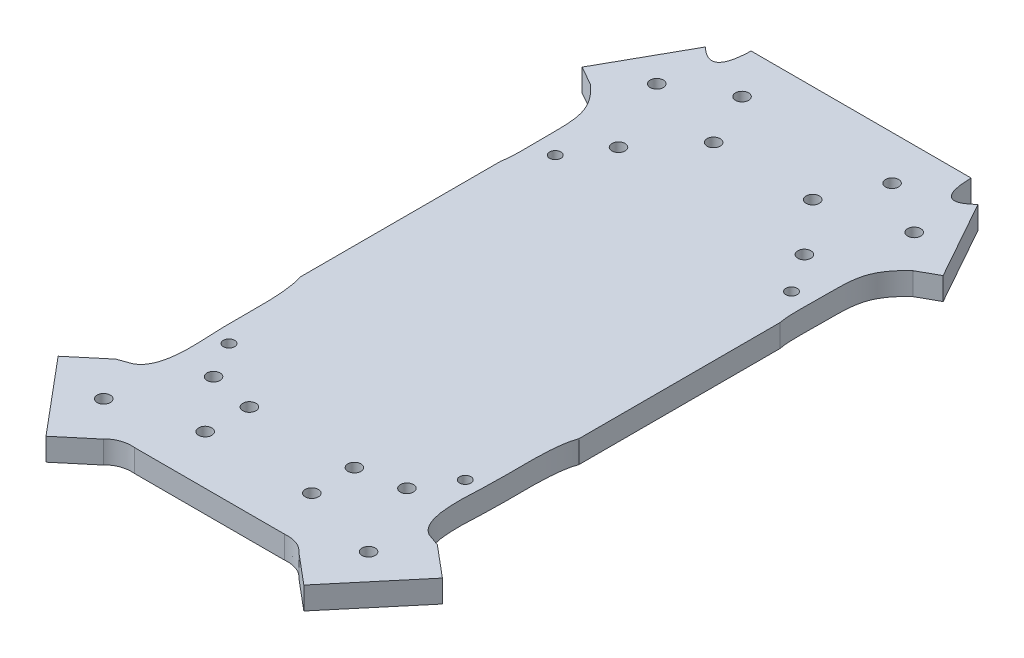
SolidWorks part; units mm, degrees
ref_plane "Front Plane" through (0, 0, 0) normal (0, 0, 1) x (1, 0, 0)
ref_plane "Top Plane" through (0, 0, 0) normal (0, 1, 0) x (1, 0, 0)
ref_plane "Right Plane" through (0, 0, 0) normal (1, 0, 0) x (0, 0, -1)
sketch "Sketch1" plane through (0, 0, 0) normal (0, 1, 0) x (1, 0, 0)
  line L1 (0, 0) -> (200, 0)
  line L2 (0, 0) -> (0, 250)
  line L3 (0, 250) -> (200, 250)
  line L4 (200, 0) -> (200, 250)
  dimension "D1" = 250
  dimension "D2" = 200
extrude "Boss-Extrude1" add sketch "Sketch1" along normal blind 6
hole_wizard "Ø3.0mm Dowel Hole1" positions "Sketch4" profile "Sketch5" hole size "Ø3.0" standard "ANSI Metric" end condition through all
sketch "Sketch4" plane through (0, 0, 0) normal (0, -1, 0) x (-1, 0, 0)
  point P0 (-83.2968, 150.1379)
  point P3 (-94.867, 163.9267)
  point P6 (-121.2968, 163.9267)
  point P9 (-132.867, 150.1379)
  point P12 (-128.0819, 178.2926)
  point P15 (-142.4028, 169.8881)
  point P18 (-88.0819, 178.2926)
  point P21 (-73.761, 169.8881)
  point P24 (-133.867, 43.1379)
  point P27 (-122.0819, 40.922)
  point P30 (-122.2968, 29.3491)
  point P33 (-94.0819, 40.922)
  point P36 (-93.867, 29.3491)
  point P39 (-82.2968, 43.1379)
  point P42 (-72.761, 23.3877)
  point P45 (-143.4028, 23.3877)
  point P51 (-128.0819, 170.5038)
  point P56 (-72.3135, 72.4419)
  point P61 (-77.6564, 46.709)
  dimension "D1" = 9.5358
  dimension "D2" = 19.7502
  dimension "D3" = 14.3209
  dimension "D4" = 8.4046
  dimension "D5" = 14.3659
  dimension "D6" = 6.7851
  dimension "D7" = 26.4298
  dimension "D8" = 14.3659
  dimension "D9" = 14.3209
  dimension "D10" = 8.4046
  dimension "D11" = 19.7502
  dimension "D12" = 9.5358
  dimension "D13" = 11.5702
  dimension "D14" = 13.7888
  dimension "D15" = 11.7851
  dimension "D16" = 2.2159
  dimension "D17" = 11.5729
  dimension "D18" = 21.106
  dimension "D19" = 5.9614
  dimension "D20" = 21.3209
  dimension "D21" = 11.5729
  dimension "D22" = 11.5702
  dimension "D23" = 11.7851
  dimension "D24" = 2.2159
  dimension "D25" = 19.7502
  dimension "D26" = 9.5358
  dimension "D27" = 28
  dimension "D28" = 11.5729
  dimension "D29" = 107
sketch "Sketch5" plane through (83.2968, 0, -150.1379) normal (1, 0, 0) x (0, 0, -1)
  line L0 (0, 0) -> (0, 6)
  line L1 (0, 6) -> (1.75, 6)
  line L2 (1.75, 6) -> (1.75, 0)
  line L5 (1.75, 0) -> (0, 0)
  line L11 (0, -6.35) -> (0, 107.95) construction
  dimension "Thru Hole Dia." = 3.5
  dimension "Thru Hole Depth" = 6
sketch "Sketch6" plane through (0, 0, 0) normal (0, -1, 0) x (1, 0, 0)
  line L0 (125.0968, -27.7325) -> (122.2968, -26.1159)
  line L1 (122.2968, -26.1159) -> (119.4968, -27.7325)
  line L2 (119.4968, -27.7325) -> (119.4968, -30.9657)
  line L3 (132.867, -153.3711) -> (132.867, -146.9047) construction
  line L4 (135.667, -150.1379) -> (130.067, -150.1379) construction
  line L5 (119.4968, -30.9657) -> (122.2968, -32.5823)
  line L6 (122.2968, -32.5823) -> (125.0968, -30.9657)
  line L7 (125.0968, -30.9657) -> (125.0968, -27.7325)
  line L8 (133.867, -39.9047) -> (131.067, -41.5213)
  line L9 (131.067, -41.5213) -> (131.067, -44.7545)
  line L10 (131.067, -44.7545) -> (133.867, -46.3711)
  line L11 (133.867, -46.3711) -> (136.667, -44.7545)
  line L12 (136.667, -44.7545) -> (136.667, -41.5213)
  line L13 (136.667, -41.5213) -> (133.867, -39.9047)
  line L19 (121.2968, -167.1599) -> (121.2968, -160.6935) construction
  line L22 (82.2968, -39.9047) -> (79.4968, -41.5213)
  line L23 (79.4968, -41.5213) -> (79.4968, -44.7545)
  line L24 (79.4968, -44.7545) -> (82.2968, -46.3711)
  line L25 (118.4968, -163.9267) -> (124.0968, -163.9267) construction
  line L26 (82.2968, -46.3711) -> (85.0968, -44.7545)
  line L27 (85.0968, -44.7545) -> (85.0968, -41.5213)
  line L28 (94.867, -167.1599) -> (94.867, -160.6935) construction
  line L29 (97.667, -163.9267) -> (92.067, -163.9267) construction
  line L30 (85.0968, -41.5213) -> (82.2968, -39.9047)
  line L31 (93.867, -26.1159) -> (91.067, -27.7325)
  line L32 (83.2968, -153.3711) -> (83.2968, -146.9047) construction
  line L33 (80.4968, -148.5213) -> (86.0968, -151.7545) construction
  line L34 (91.067, -27.7325) -> (91.067, -30.9657)
  line L35 (80.4968, -151.7545) -> (86.0968, -148.5213) construction
  line L36 (91.067, -30.9657) -> (93.867, -32.5823)
  line L37 (93.867, -32.5823) -> (96.667, -30.9657)
  line L38 (96.667, -30.9657) -> (96.667, -27.7325)
  line L39 (96.667, -27.7325) -> (93.867, -26.1159)
  line L40 (94.867, -160.6935) -> (92.067, -162.3101)
  line L41 (92.067, -162.3101) -> (92.067, -165.5433)
  line L42 (92.067, -165.5433) -> (94.867, -167.1599)
  line L43 (94.867, -167.1599) -> (97.667, -165.5433)
  line L44 (97.667, -165.5433) -> (97.667, -162.3101)
  line L45 (97.667, -162.3101) -> (94.867, -160.6935)
  line L46 (83.2968, -146.9047) -> (80.4968, -148.5213)
  line L47 (80.4968, -148.5213) -> (80.4968, -151.7545)
  line L48 (80.4968, -151.7545) -> (83.2968, -153.3711)
  line L49 (83.2968, -153.3711) -> (86.0968, -151.7545)
  line L50 (86.0968, -151.7545) -> (86.0968, -148.5213)
  line L51 (86.0968, -148.5213) -> (83.2968, -146.9047)
  line L52 (121.2968, -160.6935) -> (118.4968, -162.3101)
  line L53 (118.4968, -162.3101) -> (118.4968, -165.5433)
  line L54 (118.4968, -165.5433) -> (121.2968, -167.1599)
  line L55 (121.2968, -167.1599) -> (124.0968, -165.5433)
  line L56 (124.0968, -165.5433) -> (124.0968, -162.3101)
  line L57 (124.0968, -162.3101) -> (121.2968, -160.6935)
  line L58 (132.867, -153.3711) -> (135.667, -151.7545)
  line L59 (135.667, -151.7545) -> (135.667, -148.5213)
  line L60 (135.667, -148.5213) -> (132.867, -146.9047)
  line L61 (132.867, -146.9047) -> (130.067, -148.5213)
  line L62 (130.067, -148.5213) -> (130.067, -151.7545)
  line L63 (130.067, -151.7545) -> (132.867, -153.3711)
  line L64 (84.6968, -152.5628) -> (81.8968, -147.713) construction
  circle A0 centre (132.867, -150.1379) radius 1.75 construction
  circle A1 centre (121.2968, -163.9267) radius 1.75 construction
  circle A2 centre (94.867, -163.9267) radius 1.75 construction
  circle A3 centre (83.2968, -150.1379) radius 1.75 construction
  circle A4 centre (132.867, -150.1379) radius 1.75
  circle A5 centre (121.2968, -163.9267) radius 1.75
  circle A6 centre (94.867, -163.9267) radius 1.75
  circle A7 centre (83.2968, -150.1379) radius 1.75
  point P32 (132.867, -150.1379)
  point P34 (121.2968, -163.9267)
  point P35 (94.867, -163.9267)
  point P36 (83.2968, -150.1379)
  dimension "D1" = 0
  dimension "D2" = 0
  dimension "D3" = 0
  dimension "D4" = 0
extrude "Cut-Extrude3" cut sketch "Sketch6" against normal blind 2.2
sketch "Sketch2" plane through (0, 0, 0) normal (0, -1, 0) x (1, 0, 0)
  line L0 (143.2063, -38.4743) -> (139.3486, -82.5678)
  line L1 (78.0819, -97.0459) -> (75.3007, -149.8321)
  line L2 (138.3335, -94.1709) -> (138.0819, -97.0459)
  line L4 (70.1946, -158.0343) -> (59.933, -163.7716)
  line L5 (128.0819, -16.2435) -> (88.0819, -16.2435)
  line L6 (59.933, -163.7716) -> (71.7231, -184.8593)
  line L8 (72.9576, -38.4743) -> (76.8153, -82.5678)
  line L10 (77.8304, -94.1709) -> (78.0819, -97.0459)
  line L13 (78.761, -190.0363) -> (137.4028, -190.0363)
  line L16 (108.0819, -16.2435) -> (108.0819, -190.0363) construction
  line L19 (73.761, -169.8881) -> (79.6595, -180.438) construction
  line L21 (71.8743, -36.5483) -> (65.2141, -34.1729)
  line L22 (65.2141, -34.1729) -> (56.8447, -27.1502)
  line L23 (56.8447, -27.1502) -> (73.7024, -7.0599)
  line L24 (73.761, -169.8881) -> (67.8626, -159.3381) construction
  line L25 (73.7024, -7.0599) -> (82.0719, -14.0827)
  line L26 (156.2309, -163.7716) -> (144.4407, -184.8593)
  line L37 (142.4614, -7.0599) -> (134.092, -14.0827)
  line L38 (159.3191, -27.1502) -> (142.4614, -7.0599)
  line L39 (150.9497, -34.1729) -> (159.3191, -27.1502)
  line L40 (144.2896, -36.5483) -> (150.9497, -34.1729)
  line L49 (0, 0) -> (0, -253.5195)
  line L50 (200, 0) -> (0, 0)
  line L51 (200, -253.5195) -> (200, 0)
  line L52 (0, -253.5195) -> (200, -253.5195)
  line L53 (142.4028, -169.8881) -> (148.3013, -159.3381) construction
  line L54 (145.9692, -158.0343) -> (156.2309, -163.7716)
  line L55 (138.0819, -97.0459) -> (140.8631, -149.8321)
  arc A0 (138.3335, -94.1709) -> (139.3486, -82.5678) centre (137.4028, -88.2435) ccw
  arc A1 (76.8153, -82.5678) -> (77.8304, -94.1709) centre (78.761, -88.2435) ccw
  arc A2 (145.9692, -158.0343) -> (140.8631, -149.8321) centre (150.8493, -149.3059) cw
  arc A3 (75.3007, -149.8321) -> (70.1946, -158.0343) centre (65.3146, -149.3059) cw
  spline S0 degree 2 poles (71.7231, -184.8593) (78.4774, -178.411) (78.761, -190.0363) knots 0 0 0 1 1 1
  spline S1 degree 2 poles (144.4407, -184.8593) (137.6864, -178.411) (137.4028, -190.0363) knots 0 0 0 1 1 1
  spline S6 degree 3 poles (134.092, -14.0827) (132.6324, -15.7971) (130.2548, -16.4555) (128.0819, -16.2435) knots 0 0 0 0 1 1 1 1
  spline S7 degree 3 poles (82.0719, -14.0827) (83.5315, -15.7971) (85.9091, -16.4555) (88.0819, -16.2435) knots 0 0 0 0 1 1 1 1
  spline S8 degree 3 poles (71.8743, -36.5483) (73.0299, -36.4607) (72.9809, -37.7548) (72.9576, -38.4743) knots 0 0 0 0 1 1 1 1
  spline S9 degree 3 poles (144.2896, -36.5483) (143.1339, -36.4607) (143.1829, -37.7548) (143.2063, -38.4743) knots 0 0 0 0 1 1 1 1
  point P34 (141.1534, -155.3418)
  point P37 (75.0104, -155.3418)
  point P90 (147.6197, -35.3606)
  dimension "D2" = 10
extrude "Cut-Extrude2" cut sketch "Sketch2" against normal through all both and the other way through all
sketch "Sketch12" plane through (0, 0, 0) normal (0, -1, 0) x (1, 0, 0)
  line L0 (144.2896, -36.5483) -> (150.9497, -34.1729) construction
  line L1 (156.2309, -163.7716) -> (145.9692, -158.0343) construction
  line L2 (145.3338, -131.1814) -> (145.3338, -77.629)
  line L3 (139.3486, -82.5678) -> (143.2063, -38.4743) construction
  line L4 (138.0819, -97.0459) -> (138.3335, -94.1709) construction
  line L5 (140.8631, -149.8321) -> (138.0819, -97.0459) construction
  line L6 (144.2896, -36.5483) -> (147.6197, -35.3606)
  line L7 (139.3486, -82.5678) -> (143.2063, -38.4743)
  line L8 (138.0819, -97.0459) -> (138.3335, -94.1709)
  line L9 (140.8631, -149.8321) -> (138.0819, -97.0459)
  line L10 (151.1, -160.9029) -> (145.9692, -158.0343)
  line L11 (108.0819, -16.2435) -> (108.0819, -33.949) construction
  line L12 (128.0819, -16.2435) -> (88.0819, -16.2435) construction
  line L13 (70.8301, -131.1814) -> (70.8301, -77.629)
  line L14 (71.8743, -36.5483) -> (68.5442, -35.3606)
  line L15 (76.8153, -82.5678) -> (72.9576, -38.4743)
  line L16 (78.0819, -97.0459) -> (77.8304, -94.1709)
  line L17 (75.3007, -149.8321) -> (78.0819, -97.0459)
  line L18 (65.0638, -160.9029) -> (70.1946, -158.0343)
  arc A4 (138.3335, -94.1709) -> (139.3486, -82.5678) centre (137.4028, -88.2435) ccw construction
  arc A5 (140.8631, -149.8321) -> (145.9692, -158.0343) centre (150.8493, -149.3059) ccw construction
  arc A6 (138.3335, -94.1709) -> (139.3486, -82.5678) centre (137.4028, -88.2435) ccw
  arc A7 (140.8631, -149.8321) -> (145.9692, -158.0343) centre (150.8493, -149.3059) ccw
  arc A8 (77.8304, -94.1709) -> (76.8153, -82.5678) centre (78.761, -88.2435) cw
  arc A9 (75.3007, -149.8321) -> (70.1946, -158.0343) centre (65.3146, -149.3059) cw
  spline S0 degree 3 poles (147.6197, -35.3606) (142.7772, -37.9268) (144.389, -55.6985) (143.7907, -63.4168) (144.2414, -74.5451) (145.3338, -77.629) knots 0 0 0 0 0.389986 0.710399 0.928446 0.928446 0.928446 0.928446
  spline S1 degree 3 poles (151.1, -160.9029) (144.2313, -154.6959) (145.4212, -148.8537) (144.801, -133.7083) (145.3338, -131.1814) knots 0 0 0 0 0.606255 0.822011 0.822011 0.822011 0.822011
  spline S2 degree 3 poles (-1380.1109, 2545.7291) (1722.7983, -2623.3948) (-1493.6812, 2510.9376) (1838.359, -2511.9459) knots -10.718943 -10.718943 -10.718943 -10.718943 11.150048 11.150048 11.150048 11.150048 only from (143.2063, -38.4743) to (144.2896, -36.5483) construction
  spline S3 degree 3 poles (143.2063, -38.4743) (143.1829, -37.7548) (143.1339, -36.4607) (144.2896, -36.5483) knots 0 0 0 0 1 1 1 1
  spline S4 degree 3 poles (65.0638, -160.9029) (71.9325, -154.6959) (70.7427, -148.8537) (71.3628, -133.7083) (70.8301, -131.1814) knots 0 0 0 0 0.606255 0.822011 0.822011 0.822011 0.822011
  spline S5 degree 3 poles (68.5442, -35.3606) (73.3866, -37.9268) (71.7749, -55.6985) (72.3732, -63.4168) (71.9225, -74.5451) (70.8301, -77.629) knots 0 0 0 0 0.389986 0.710399 0.928446 0.928446 0.928446 0.928446
  spline S6 degree 3 poles (72.9576, -38.4743) (72.9809, -37.7548) (73.0299, -36.4607) (71.8743, -36.5483) knots 0 0 0 0 1 1 1 1
extrude "Boss-Extrude3" add sketch "Sketch12" against normal up to surface (6 mm away) up to face at (143.4028, 6, -25.1377)
sketch "Sketch13" plane through (0, 0, 0) normal (0, -1, 0) x (1, 0, 0)
  circle A0 centre (139.6954, -52.8711) radius 1.5
  circle A1 centre (76.6954, -52.8711) radius 1.5
  circle A2 centre (76.6954, -139.8711) radius 1.5
  circle A5 centre (139.6954, -139.8711) radius 1.5
extrude "Cut-Extrude4" cut sketch "Sketch13" against normal through all both and the other way through all
